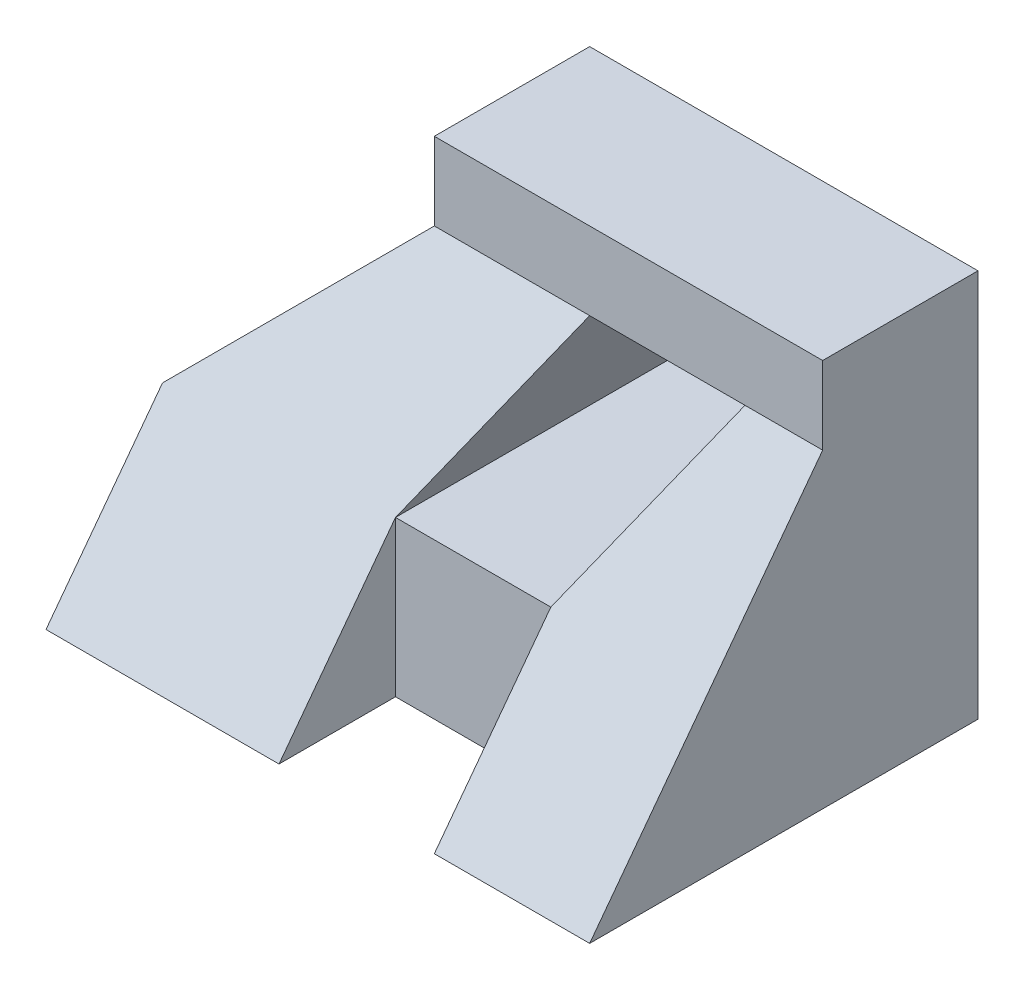
SolidWorks part; units mm, degrees
ref_plane "Front Plane" through (0, 0, 0) normal (0, 0, 1) x (1, 0, 0)
ref_plane "Top Plane" through (0, 0, 0) normal (0, 1, 0) x (1, 0, 0)
ref_plane "Right Plane" through (0, 0, 0) normal (1, 0, 0) x (0, 0, -1)
sketch "Sketch1" plane through (0, 0, 0) normal (0, 0, 1) x (1, 0, 0)
  line L0 (0, 0) -> (0, 20)
  line L1 (0, 20) -> (20, 40)
  line L2 (20, 40) -> (70, 40)
  line L3 (70, 40) -> (70, 0)
  line L4 (70, 0) -> (0, 0)
  dimension "D1" = 70
  dimension "D2" = 20
  dimension "D3" = 40
  dimension "D4" = 50
extrude "Boss-Extrude1" add sketch "Sketch1" along normal blind 50
sketch "Sketch2" plane through (0, 0, 50) normal (0, 0, 1) x (1, 0, 0)
  line L0 (0, 0) -> (70, 0) construction
  line L1 (50, 0) -> (30, 0)
  line L2 (50, 0) -> (50, 20)
  line L3 (50, 20) -> (30, 20)
  line L4 (30, 0) -> (30, 20)
  dimension "D1" = 20
  dimension "D2" = 20
  dimension "D3" = 20
extrude "Cut-Extrude1" cut sketch "Sketch2" against normal blind 20
sketch "Sketch3" plane through (0, 0, 50) normal (0, 0, 1) x (1, 0, 0)
  line L0 (30, 20) -> (40, 40)
  line L1 (70, 40) -> (20, 40) construction
  line L2 (40, 40) -> (60, 40)
  line L3 (50, 20) -> (60, 40)
  line L4 (30, 20) -> (50, 20)
  dimension "D1" = 30
  dimension "D2" = 10
extrude "Cut-Extrude2" cut sketch "Sketch3" against normal blind 10
sketch "Sketch4" plane through (0, 0, 50) normal (0, 0, 1) x (1, 0, 0)
  line L1 (70, 40) -> (20, 40)
  line L2 (70, 40) -> (70, 50)
  line L3 (70, 50) -> (20, 50)
  line L4 (20, 40) -> (20, 50)
  dimension "D1" = 50
  dimension "D2" = 10
extrude "Boss-Extrude2" add sketch "Sketch4" against normal blind 50
sketch "Sketch5" plane through (0, 0, 50) normal (0, 0, 1) x (1, 0, 0)
  line L0 (70, 0) -> (70, 50) construction
  line L1 (20, 50) -> (70, 50)
  line L2 (20, 50) -> (20, 40)
  line L3 (20, 40) -> (70, 40)
  line L4 (70, 50) -> (70, 40)
  dimension "D1" = 10
extrude "Cut-Extrude5" cut sketch "Sketch5" against normal blind 30
sketch "Sketch6" plane through (0, 0, 30) normal (0, 0, 1) x (1, 0, 0)
  line L1 (30, 20) -> (50, 20)
  line L2 (30, 20) -> (30, 0)
  line L3 (30, 0) -> (50, 0)
  line L4 (50, 20) -> (50, 0)
extrude "Boss-Extrude4" add sketch "Sketch6" along normal blind 5
sketch "Sketch8" plane through (0, 0, 40) normal (0, 0, 1) x (1, 0, 0)
  line L0 (40, 40) -> (60, 40)
  line L1 (50, 20) -> (60, 40) construction
  line L2 (60, 40) -> (40, 40) construction
  line L3 (60, 40) -> (50, 20)
  line L4 (50, 20) -> (30, 20)
  line L5 (30, 20) -> (40, 40)
extrude "Cut-Extrude8" cut sketch "Sketch8" against normal blind 40
sketch "Sketch9" plane through (0, 0, 0) normal (-1, 0, 0) x (0, 0, 1)
  line L0 (50, 0) -> (20, 40)
  line L1 (20, 40) -> (50, 40)
  line L2 (50, 0) -> (50, 40)
  line M3 (50, 0) -> (50, 20)
  line M4 (50, 20) -> (0, 20)
  dimension "D1" = 20
  dimension "D2" = 30
  dimension "D3" = 40
extrude "Cut-Extrude9" cut sketch "Sketch9" against normal blind 70 contours L2 L1 L0 M4 | L0 M3 M4
